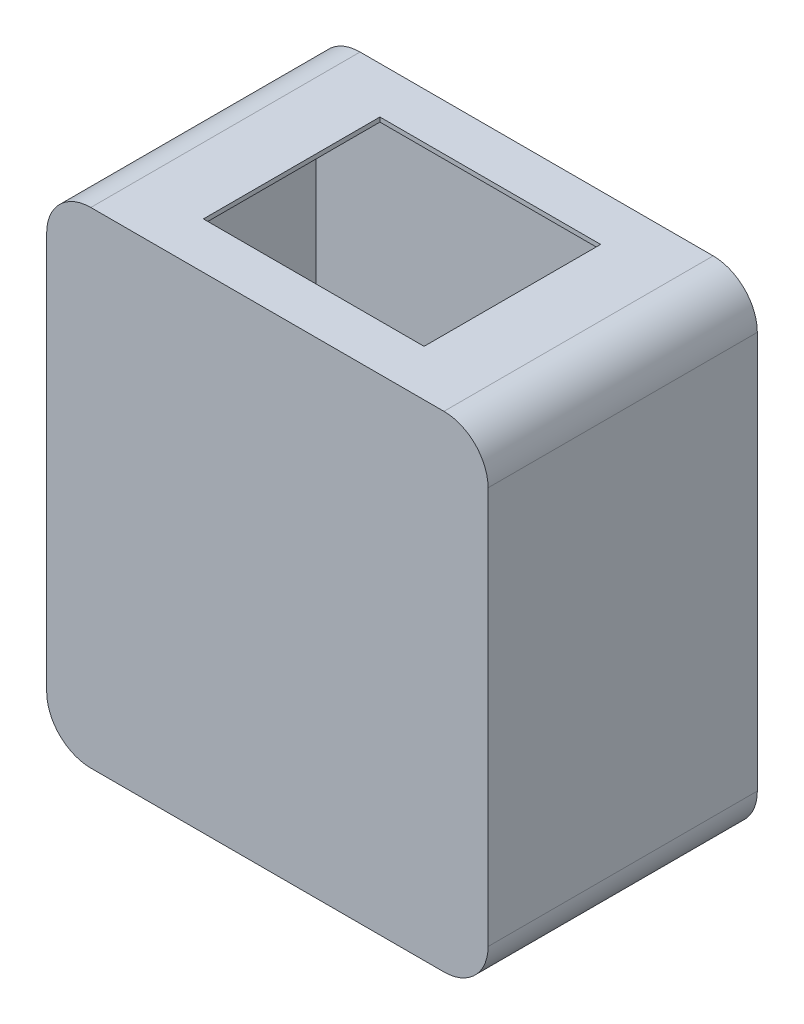
SolidWorks part; units mm, degrees
ref_plane "Front Plane" through (0, 0, 0) normal (0, 0, 1) x (1, 0, 0)
ref_plane "Top Plane" through (0, 0, 0) normal (0, 1, 0) x (1, 0, 0)
ref_plane "Right Plane" through (0, 0, 0) normal (1, 0, 0) x (0, 0, -1)
sketch "Sketch1" plane through (0, 0, 0) normal (0, 0, 1) x (1, 0, 0)
  line L0 (-96.6152, 124.7537) -> (63.3848, 124.7537)
  line L1 (-98.6152, 126.7537) -> (61.3848, 126.7537)
  line L2 (-118.6152, 106.7537) -> (-118.6152, -73.2463)
  line L4 (81.3848, 106.7537) -> (81.3848, -73.2463)
  line L13 (-116.6152, 104.7537) -> (-116.6152, -71.0526)
  line L18 (-98.6152, -93.2463) -> (61.3848, -93.2463)
  line L19 (79.3848, 108.9474) -> (79.3848, -71.0526)
  line L21 (-110.8263, -85.3201) -> (-16.6152, -91.2463)
  line L22 (-16.6152, -91.2463) -> (75.0695, -84.069)
  arc A1 (-98.6152, 126.7537) -> (-118.6152, 106.7537) centre (-98.6152, 106.7537) ccw
  arc A2 (61.3848, 126.7537) -> (81.3848, 106.7537) centre (61.3848, 106.7537) cw
  arc A5 (61.3848, -93.2463) -> (81.3848, -73.2463) centre (61.3848, -73.2463) ccw
  arc A6 (-98.6152, -93.2463) -> (-118.6152, -73.2463) centre (-98.6152, -73.2463) cw
  arc A7 (-96.6152, 124.7537) -> (-116.6152, 104.7537) centre (-96.6152, 104.7537) ccw
  arc A8 (63.3848, 124.7537) -> (79.3848, 108.9474) centre (59.7613, 105.0847) cw
  arc A9 (75.0695, -84.069) -> (79.3848, -71.0526) centre (59.3936, -71.6486) ccw
  arc A10 (-110.8263, -85.3201) -> (-116.6152, -71.0526) centre (-96.6162, -71.2463) cw
  point P0 (0, 0)
  point P3 (-111.0442, 2.1937)
  point P6 (0.6283, -0.5654)
  point P14 (-110.416, 1.6282)
  dimension "D3" = 40
  dimension "D4" = 40
  dimension "D1" = 220
  dimension "D2" = 200
  dimension "D5" = 2
  dimension "D6" = 196
extrude "Boss-Extrude1" add sketch "Sketch1" along normal blind 120
sketch "Sketch2" plane through (0, 0, 0) normal (0, 0, -1) x (-1, 0, 0)
  line L0 (-81.3848, -73.2463) -> (-81.3848, 106.7537) construction
  line L1 (98.6152, -93.2463) -> (-61.3848, -93.2463) construction
  line L2 (118.6152, 106.7537) -> (118.6152, -73.2463) construction
  line L3 (-61.3848, 126.7537) -> (98.6152, 126.7537) construction
  line L4 (-81.3848, -73.2463) -> (-81.3848, 106.7537)
  line L5 (98.6152, -93.2463) -> (-61.3848, -93.2463)
  line L6 (118.6152, 106.7537) -> (118.6152, -73.2463)
  line L7 (-61.3848, 126.7537) -> (98.6152, 126.7537)
  arc A0 (-61.3848, 126.7537) -> (-81.3848, 106.7537) centre (-61.3848, 106.7537) ccw construction
  arc A1 (-81.3848, -73.2463) -> (-61.3848, -93.2463) centre (-61.3848, -73.2463) ccw construction
  arc A2 (98.6152, -93.2463) -> (118.6152, -73.2463) centre (98.6152, -73.2463) ccw construction
  arc A3 (118.6152, 106.7537) -> (98.6152, 126.7537) centre (98.6152, 106.7537) ccw construction
  arc A4 (-61.3848, 126.7537) -> (-81.3848, 106.7537) centre (-61.3848, 106.7537) ccw
  arc A5 (-81.3848, -73.2463) -> (-61.3848, -93.2463) centre (-61.3848, -73.2463) ccw
  arc A6 (98.6152, -93.2463) -> (118.6152, -73.2463) centre (98.6152, -73.2463) ccw
  arc A7 (118.6152, 106.7537) -> (98.6152, 126.7537) centre (98.6152, 106.7537) ccw
extrude "Boss-Extrude2" add sketch "Sketch2" along normal blind 2
ref_plane "Plane1" through (0, 0, 59) normal (0, 0, 1) x (1, 0, 0)
mirror "Mirror1" about plane through (0, 0, 59) normal (0, 0, 1) of "Boss-Extrude2"
sketch "Sketch4" plane through (0, 0, -2) normal (0, 0, -1) x (-1, 0, 0)
  line L0 (-61.3848, -93.2463) -> (98.6152, -93.2463) construction
  line L1 (18.6152, -93.2463) -> (18.6152, 126.7537) construction
  line L2 (98.6152, 126.7537) -> (-61.3848, 126.7537) construction
  circle A0 centre (18.6152, -88.0713) radius 3.175
  dimension "D1" = 6.35
  dimension "D2" = 5.175
extrude "Cut-Extrude2" cut sketch "Sketch4" against normal blind 2 contours A0
sketch "Sketch5" plane through (0, 126.7537, 0) normal (0, 1, 0) x (1, 0, 0)
  line L0 (-98.6152, 2) -> (61.3848, 2) construction
  line L1 (-68.6152, -19) -> (31.3848, -19)
  line L2 (-68.6152, -19) -> (-68.6152, -99)
  line L3 (-68.6152, -99) -> (31.3848, -99)
  line L4 (31.3848, -19) -> (31.3848, -99)
  line L5 (-68.6152, -19) -> (31.3848, -99) construction
  line L6 (-68.6152, -99) -> (31.3848, -19) construction
  line L8 (-18.6152, -120) -> (-18.6152, 2) construction
  line L9 (61.3848, -120) -> (-98.6152, -120) construction
  line L10 (-98.6152, -59) -> (61.3848, -59) construction
  line L11 (-98.6152, -120) -> (-98.6152, 2) construction
  line L12 (61.3848, -120) -> (61.3848, 2) construction
  point P0 (-18.6152, -59)
  dimension "D1" = 100
  dimension "D2" = 80
extrude "Cut-Extrude3" cut sketch "Sketch5" against normal blind 2
sketch "Sketch6" plane through (0, 0, -2) normal (0, 0, -1) x (-1, 0, 0)
  circle A0 centre (18.6152, -88.0713) radius 3.175 construction
  circle A1 centre (18.6152, -88.0713) radius 3.175
  circle A2 centre (18.6152, -88.0713) radius 1.905
  dimension "D1" = 6.35
  dimension "D2" = 3.81
extrude "Boss-Extrude3" add sketch "Sketch6" along normal blind 12.7 and the other way blind 2 separate body
equation "\"wallthickness\"= 0.2cm"
equation "\"height\"= 22cm"
equation "\"width\"= 20cm"
equation "\"D1@Sketch1\"=\"height\""
equation "\"D2@Sketch1\"=\"width\""
equation "\"D5@Sketch1\"=\"wallthickness\""
equation "\"D2@Sketch4\"=\"wallthickness\"+ 0.125in"
